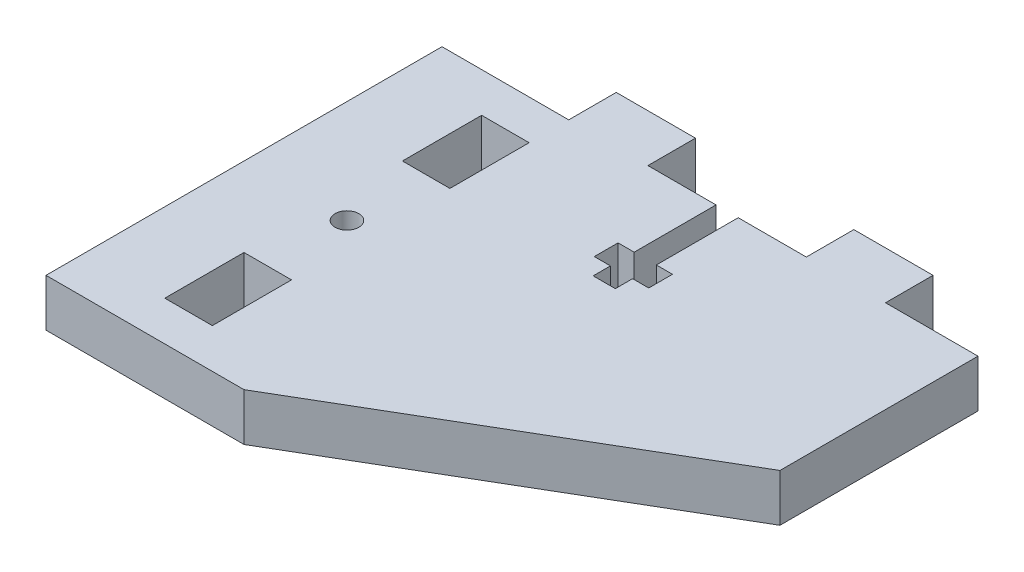
SolidWorks part; units mm, degrees
ref_plane "Спереди" through (0, 0, 0) normal (0, 0, 1) x (1, 0, 0)
ref_plane "Сверху" through (0, 0, 0) normal (0, 1, 0) x (1, 0, 0)
ref_plane "Справа" through (0, 0, 0) normal (1, 0, 0) x (0, 0, -1)
sketch "Эскиз1" plane through (0, 0, 0) normal (0, 1, 0) x (1, 0, 0)
  line L0 (-3.4168, 32.7424) -> (5.1832, 32.7424)
  line L1 (-13.4168, 38.7424) -> (-13.4168, 32.7424)
  line L2 (-3.4168, 32.7424) -> (-3.4168, 38.7424)
  line L3 (-3.4168, 38.7424) -> (-13.4168, 38.7424)
  line L4 (-4.4168, -17.2576) -> (-29.4168, -17.2576)
  line L5 (-13.4168, 27.7424) -> (-19.4168, 27.7424)
  line L6 (38.2552, 7.7424) -> (-4.4168, -17.2576)
  line L7 (-13.4168, 17.7424) -> (-13.4168, 27.7424)
  line L8 (-19.4168, 27.7424) -> (-19.4168, 17.7424)
  line L9 (-19.4168, 17.7424) -> (-13.4168, 17.7424)
  line L10 (26.5832, 32.7424) -> (26.5832, 38.7424)
  line L11 (16.5832, 38.7424) -> (16.5832, 32.7424)
  line L12 (26.5832, 38.7424) -> (16.5832, 38.7424)
  line L13 (26.5832, 32.7424) -> (38.2594, 32.7424)
  line L14 (-13.4168, -12.2576) -> (-13.4168, -2.2576)
  line L15 (-19.4168, -12.2576) -> (-13.4168, -12.2576)
  line L16 (-13.4168, -2.2576) -> (-19.4168, -2.2576)
  line L17 (-19.4168, -2.2576) -> (-19.4168, -12.2576)
  line L18 (38.2594, 32.7424) -> (38.2552, 7.7424)
  line L19 (-29.4168, 32.7424) -> (-13.4168, 32.7424)
  line L20 (-29.4168, -17.2576) -> (-29.4168, 32.7424)
  line L21 (5.1841, 17.2259) -> (7.9841, 17.2276)
  line L22 (7.9828, 19.4065) -> (10.0203, 19.4077)
  line L23 (5.1832, 32.7424) -> (5.1832, 22.4072)
  line L24 (7.9841, 17.2276) -> (7.9828, 19.4065)
  line L25 (10.0203, 19.4077) -> (10.0204, 22.407)
  line L26 (10.0204, 22.407) -> (7.9832, 22.4071)
  line L27 (3.1466, 19.4066) -> (5.1828, 19.4078)
  line L28 (3.1467, 22.4072) -> (3.1466, 19.4066)
  line L29 (5.1832, 22.4072) -> (3.1467, 22.4072)
  line L30 (5.1828, 19.4078) -> (5.1841, 17.2259)
  line L31 (7.9832, 22.4071) -> (7.9832, 32.7424)
  line L32 (7.9832, 32.7424) -> (16.5832, 32.7424)
  line L33 (-64.3952, 32.7424) -> (50.48, 32.7424) construction
  circle A0 centre (-16.4168, 7.7424) radius 1.5
  point P35 (9.0018, 22.4071)
  point P36 (4.1647, 19.4072)
  dimension "D7" = 3
  dimension "D1" = 16
  dimension "D3" = 6
  dimension "D4" = 50
  dimension "D5" = 6
  dimension "D6" = 2.8
  dimension "D8" = 2.8
  dimension "D9" = 3
  dimension "D10" = 3
  dimension "D11" = 10
  dimension "D12" = 10
  dimension "D13" = 8.6
  dimension "D14" = 8.6
  dimension "D15" = 10
  dimension "D16" = 10
  dimension "D17" = 6
  dimension "D18" = 5
  dimension "D19" = 10
  dimension "D20" = 13
  dimension "D21" = 6
  dimension "D22" = 10
  dimension "D23" = 10
  dimension "D24" = 10
  dimension "D25" = 25
  dimension "D26" = 25
extrude "Бобышка-Вытянуть2" add sketch "Эскиз1" along normal blind 6
